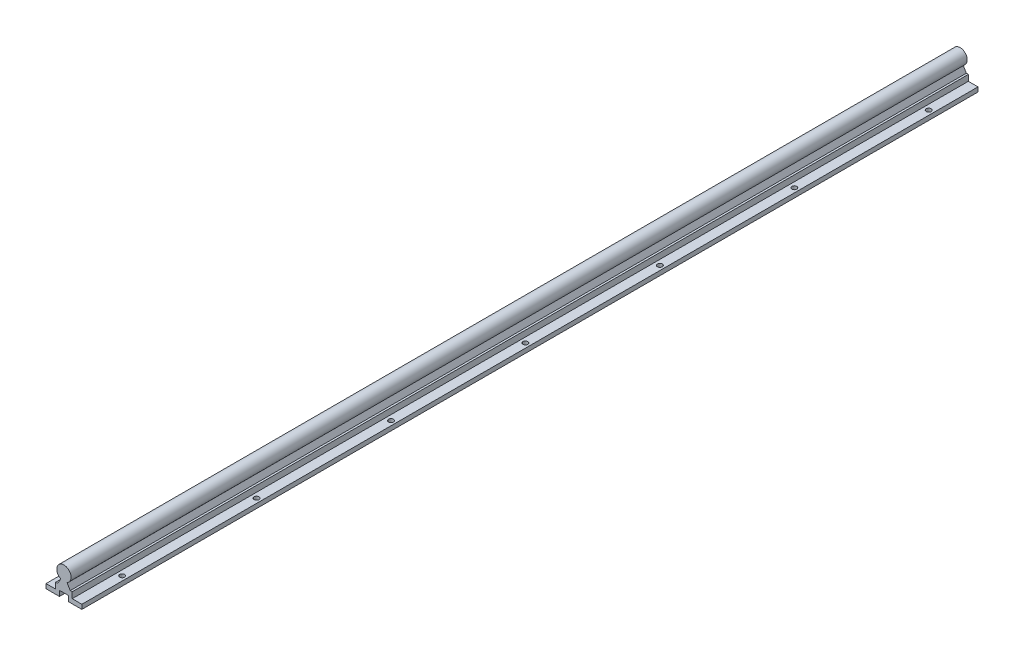
SolidWorks part; units mm, degrees
ref_plane "Front Plane" through (0, 0, 0) normal (0, 0, 1) x (1, 0, 0)
ref_plane "Top Plane" through (0, 0, 0) normal (0, 1, 0) x (1, 0, 0)
ref_plane "Right Plane" through (0, 0, 0) normal (1, 0, 0) x (0, 0, -1)
sketch "Sketch1" plane through (0, 0, 0) normal (0, 0, 1) x (1, 0, 0)
  line L0 (-7.009, -13.3) -> (-3.4871, -7.2)
  line L1 (0, 0) -> (0, -25) construction
  line L2 (3.4871, -7.2) -> (7.009, -13.3)
  line L3 (-9.25, -13.3) -> (-7.009, -13.3)
  line L4 (7.009, -13.3) -> (9.25, -13.3)
  line L5 (9.25, -13.3) -> (9.25, -20)
  line L6 (9.25, -20) -> (20, -20)
  line L7 (20, -20) -> (20, -25)
  line L8 (20, -25) -> (5, -25)
  line L9 (5, -25) -> (5, -19)
  line L10 (5, -19) -> (-5, -19)
  line L11 (-5, -19) -> (-5, -25)
  line L12 (-5, -25) -> (-20, -25)
  line L13 (-20, -25) -> (-20, -20)
  line L14 (-20, -20) -> (-9.25, -20)
  line L15 (-9.25, -20) -> (-9.25, -13.3)
  arc A0 (3.4871, -7.2) -> (-3.4871, -7.2) centre (0, 0) ccw
  dimension "D2" = 16
  dimension "D1" = 60
  dimension "D3" = 11.7
  dimension "D4" = 5
  dimension "D5" = 17.8
  dimension "D6" = 40
  dimension "D7" = 18.5
  dimension "D8" = 25
  dimension "D9" = 10
  dimension "D10" = 6
extrude "Boss-Extrude1" add sketch "Sketch1" along normal mid plane 1000
sketch "Sketch2" plane through (0, -20, 0) normal (0, 1, 0) x (1, 0, 0)
  line L0 (-15, -450) -> (15, -450) construction
  line L1 (0, 0) -> (0, -450) construction
  line L2 (-8, -500) -> (8, -500) construction
  circle A0 centre (15, -450) radius 2.75
  circle A1 centre (-15, -450) radius 2.75
  dimension "D2" = 5.5
  dimension "D1" = 30
  dimension "D3" = 50
extrude "Cut-Extrude1" cut sketch "Sketch2" against normal through all
pattern_linear "LPattern1" count 7 spacing 150 along (0, 0, -1) of "Cut-Extrude1"
